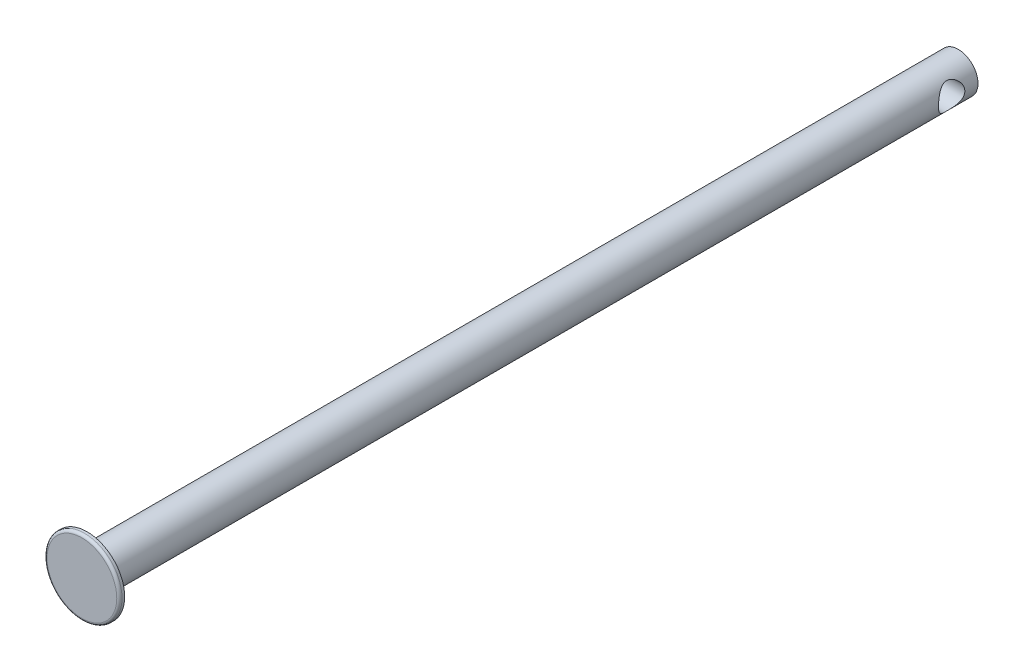
SolidWorks part; units mm, degrees
material "1.0558 (G300)"
ref_plane "Ön Düzlem" through (0, 0, 0) normal (0, 0, 1) x (1, 0, 0)
ref_plane "Üst Düzlem" through (0, 0, 0) normal (0, 1, 0) x (1, 0, 0)
ref_plane "Sağ Düzlem" through (0, 0, 0) normal (1, 0, 0) x (0, 0, -1)
sketch "Çizim1" plane through (0, 0, 0) normal (0, 0, 1) x (1, 0, 0)
  circle A0 centre (0, 0) radius 7.5
  dimension "D1" = 15
extrude "Yükseklik-Ekstrüzyon1" add sketch "Çizim1" along normal blind 331
sketch "Çizim2" plane through (0, 0, 331) normal (0, 0, 1) x (1, 0, 0)
  circle A0 centre (0, 0) radius 14.25
  dimension "D1" = 28.5
extrude "Yükseklik-Ekstrüzyon2" add sketch "Çizim2" along normal blind 2
fillet "Radyus1" radius 1 1 edges at (14.25, 0, 333)
ref_plane "Düzlem1" through (0, 0, 5) normal (0, 0, -1) x (-1, 0, 0)
sketch "Çizim6" plane through (0, 0, 0) normal (1, 0, 0) x (0, 0, -1)
  line L1 (-5, -8.25) -> (-5, 8.25) construction
  circle A1 centre (-10, 0) radius 5
  dimension "D1" = 10
extrude "Kes-Ekstrüzyon1" cut sketch "Çizim6" against normal mid plane 44
